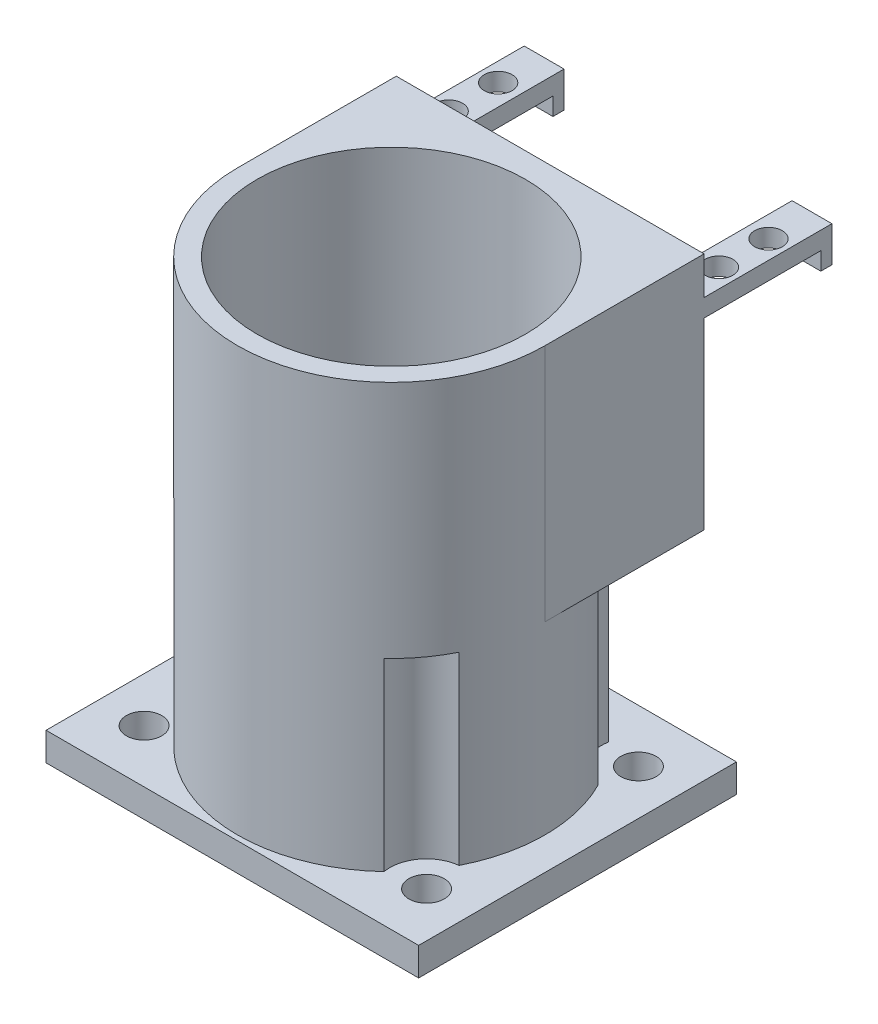
SolidWorks part; units mm, degrees
ref_plane "Front Plane" through (0, 0, 0) normal (0, 0, 1) x (1, 0, 0)
ref_plane "Top Plane" through (0, 0, 0) normal (0, 1, 0) x (1, 0, 0)
ref_plane "Right Plane" through (0, 0, 0) normal (1, 0, 0) x (0, 0, -1)
sketch "Sketch1" plane through (0, 0, 0) normal (0, 1, 0) x (1, 0, 0)
  line L0 (0, -9.525) -> (8.1, -9.525) construction
  line L1 (0, 0) -> (67, 0)
  line L2 (0, 0) -> (0, -57.15)
  line L3 (0, -57.15) -> (67, -57.15)
  line L4 (67, 0) -> (67, -57.15)
  line L5 (58.9, -9.525) -> (67, -9.525) construction
  line L6 (0, -28.575) -> (67, -28.575) construction
  circle A0 centre (8.1, -9.525) radius 3.175
  circle A1 centre (58.9, -9.525) radius 3.175
  circle A4 centre (58.9, -47.625) radius 3.175
  circle A5 centre (8.1, -47.625) radius 3.175
  dimension "D3" = 50.8
  dimension "D4" = 6.35
  dimension "D1" = 67
  dimension "D2" = 57.15
  dimension "D5" = 9.525
extrude "Boss-Extrude1" add sketch "Sketch1" along normal blind 5.08
sketch "Sketch2" plane through (0, 5.08, 0) normal (0, 1, 0) x (1, 0, 0)
  line L0 (33.5, 0) -> (33.5, -57.15) construction
  line L1 (67, 0) -> (0, 0) construction
  line L2 (0, -57.15) -> (67, -57.15) construction
  line L3 (0, -28.575) -> (67, -28.575) construction
  line L4 (0, 0) -> (0, -57.15) construction
  line L5 (67, -57.15) -> (67, 0) construction
  circle A0 centre (33.5, -28.575) radius 24.13
  circle A1 centre (33.5, -28.575) radius 27.67
  dimension "D1" = 55.34
extrude "Boss-Extrude2" add sketch "Sketch2" along normal blind 76.2 contours A1 | A0
sketch "Sketch4" plane through (0, 0, 0) normal (0, 0, -1) x (-1, 0, 0)
  line L7 (-33.5, 81.28) -> (-33.5, 0) construction
  line L8 (-5.83, 81.28) -> (-61.17, 81.28) construction
  line L9 (-67, 0) -> (0, 0) construction
  line L11 (-61.17, 81.28) -> (-5.83, 81.28)
  line L12 (-61.17, 81.28) -> (-61.17, 38.28)
  line L13 (-61.17, 38.28) -> (-5.83, 38.28)
  line L14 (-5.83, 81.28) -> (-5.83, 38.28)
  dimension "D1" = 55.34
  dimension "D2" = 43
extrude "Boss-Extrude3" add sketch "Sketch4" against normal up to surface (28.575 mm away)
sketch "Sketch5" plane through (0, 0, 0) normal (0, 0, -1) x (-1, 0, 0)
  line L0 (-5.83, 38.28) -> (-5.83, 81.28) construction
  line L3 (-61.17, 74.48) -> (-5.83, 74.48) construction
  line L5 (-33.5, 81.28) -> (-33.5, 5.08) construction
  line L6 (-5.83, 81.28) -> (-61.17, 81.28) construction
  line L7 (-67, 5.08) -> (0, 5.08) construction
  line L16 (-61.17, 81.28) -> (-61.17, 38.28) construction
  line L17 (-13, 71.28) -> (-5.83, 71.28)
  line L18 (-54, 74.48) -> (-61.17, 74.48)
  line L19 (-54, 74.48) -> (-54, 71.28)
  line L20 (-54, 71.28) -> (-61.17, 71.28)
  line L21 (-61.17, 74.48) -> (-61.17, 71.28)
  line L22 (-5.83, 74.48) -> (-5.83, 71.28)
  line L23 (-13, 74.48) -> (-5.83, 74.48)
  line L24 (-13, 74.48) -> (-13, 71.28)
  line L25 (-5.83, 38.28) -> (-5.83, 81.28) construction
  dimension "D1" = 6.8
  dimension "D2" = 20.5
  dimension "D3" = 3.2
extrude "Boss-Extrude4" add sketch "Sketch5" along normal blind 21
sketch "Sketch6" plane through (0, 71.28, 0) normal (0, -1, 0) x (1, 0, 0)
  line L0 (5.83, -10.5) -> (61.17, -10.5) construction
  line L1 (5.83, -21) -> (5.83, 0) construction
  line L2 (61.17, -21) -> (61.17, 0) construction
  line L4 (33.5, 0) -> (33.5, -20) construction
  line L5 (67, 0) -> (0, 0) construction
  circle A0 centre (9.2, -6.05) radius 2.5
  circle A1 centre (57.8, -6.05) radius 2.5
  circle A3 centre (57.8, -14.95) radius 2.5
  circle A4 centre (9.2, -14.95) radius 2.5
  dimension "D3" = 5
  dimension "D1" = 24.3
  dimension "D2" = 4.45
extrude "Cut-Extrude1" cut sketch "Sketch6" against normal through all
sketch "Sketch7" plane through (0, 0, -21) normal (0, 0, -1) x (-1, 0, 0)
  line L1 (-61.17, 74.48) -> (-54, 74.48)
  line L2 (-61.17, 74.48) -> (-61.17, 71.28)
  line L3 (-61.17, 71.28) -> (-54, 71.28)
  line L4 (-54, 74.48) -> (-54, 71.28)
  line L5 (-13, 74.48) -> (-5.83, 74.48)
  line L6 (-13, 74.48) -> (-13, 71.28)
  line L7 (-13, 71.28) -> (-5.83, 71.28)
  line L8 (-5.83, 74.48) -> (-5.83, 71.28)
extrude "Boss-Extrude5" add sketch "Sketch7" along normal blind 2
sketch "Sketch8" plane through (0, 71.28, 0) normal (0, -1, 0) x (1, 0, 0)
  line L0 (5.83, -23) -> (5.83, 0) construction
  line L1 (5.83, -21) -> (13, -21)
  line L2 (5.83, -21) -> (5.83, -23)
  line L3 (5.83, -23) -> (13, -23)
  line L4 (13, -21) -> (13, -23)
  line L5 (33.5, 0) -> (33.5, -22) construction
  line L6 (67, 0) -> (0, 0) construction
  line L7 (61.17, -23) -> (54, -23)
  line L8 (54, -21) -> (54, -23)
  line L9 (61.17, -21) -> (54, -21)
  line L10 (61.17, -21) -> (61.17, -23)
  dimension "D1" = 2
extrude "Boss-Extrude6" add sketch "Sketch8" along normal blind 3.2
sketch "Sketch9" plane through (0, 5.08, 0) normal (0, 1, 0) x (1, 0, 0)
  line L0 (33.5, 0) -> (33.5, -57.15) construction
  line L1 (5.83, 0) -> (61.17, 0) construction
  line L2 (0, -57.15) -> (67, -57.15) construction
  line L3 (0, -28.575) -> (67, -28.575) construction
  line L4 (0, 0) -> (0, -57.15) construction
  line L5 (67, -57.15) -> (67, 0) construction
  circle A0 centre (8.1, -9.525) radius 6.6
  circle A1 centre (58.9, -9.525) radius 6.6
  circle A2 centre (58.9, -47.625) radius 6.6
  circle A3 centre (8.1, -47.625) radius 6.6
  dimension "D1" = 13.2
extrude "Cut-Extrude2" cut sketch "Sketch9" along normal blind 33.2
